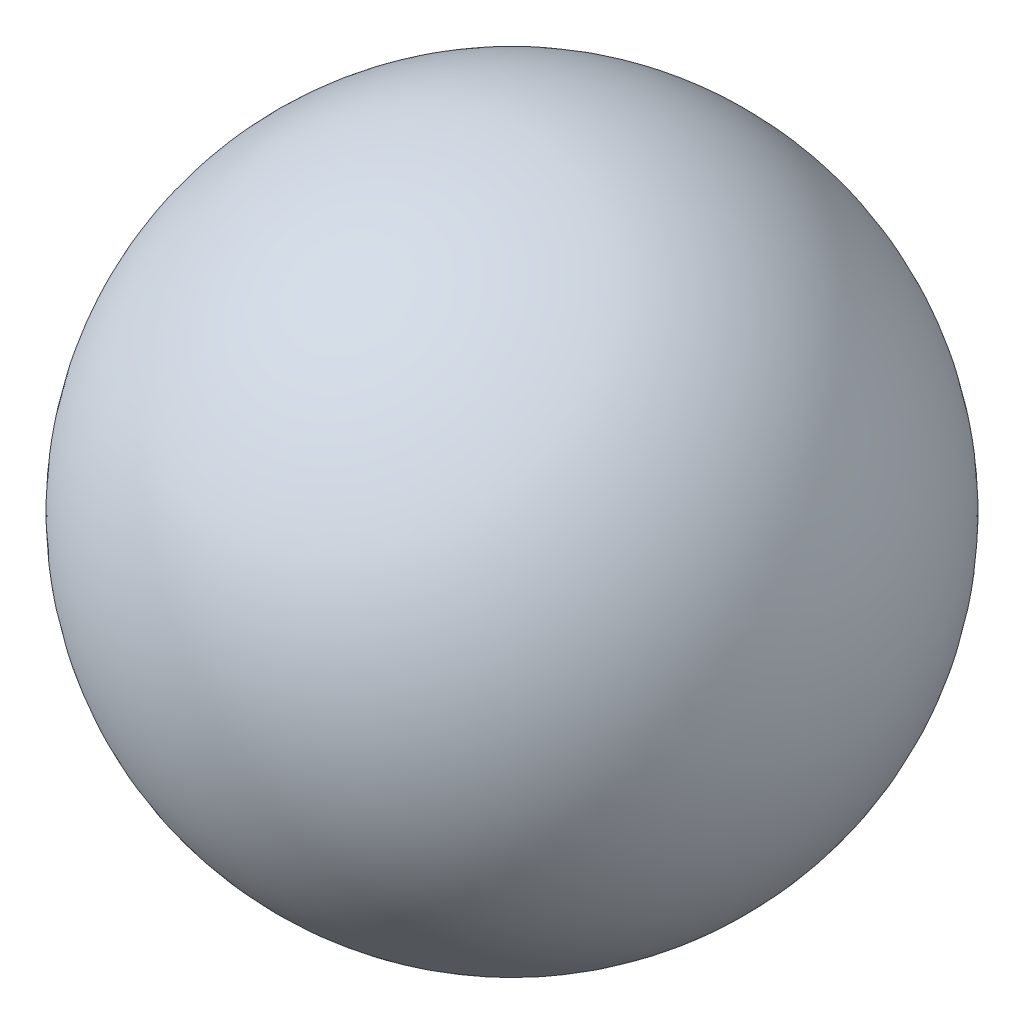
SolidWorks part; units mm, degrees
ref_plane "Front Plane" through (0, 0, 0) normal (0, 0, 1) x (1, 0, 0)
ref_plane "Top Plane" through (0, 0, 0) normal (0, 1, 0) x (1, 0, 0)
ref_plane "Right Plane" through (0, 0, 0) normal (1, 0, 0) x (0, 0, -1)
sketch "Sketch3" plane through (0, 0, 0) normal (0, 0, 1) x (1, 0, 0)
  line L0 (0, -76.2) -> (0, 76.2)
  arc A0 (0, 76.2) -> (0, -76.2) centre (-0.1622, 0) ccw
  point P4 (0, 0)
  dimension "D1" = 152.4
revolve "Revolve1" add sketch "Sketch3" angle 360 about L0
